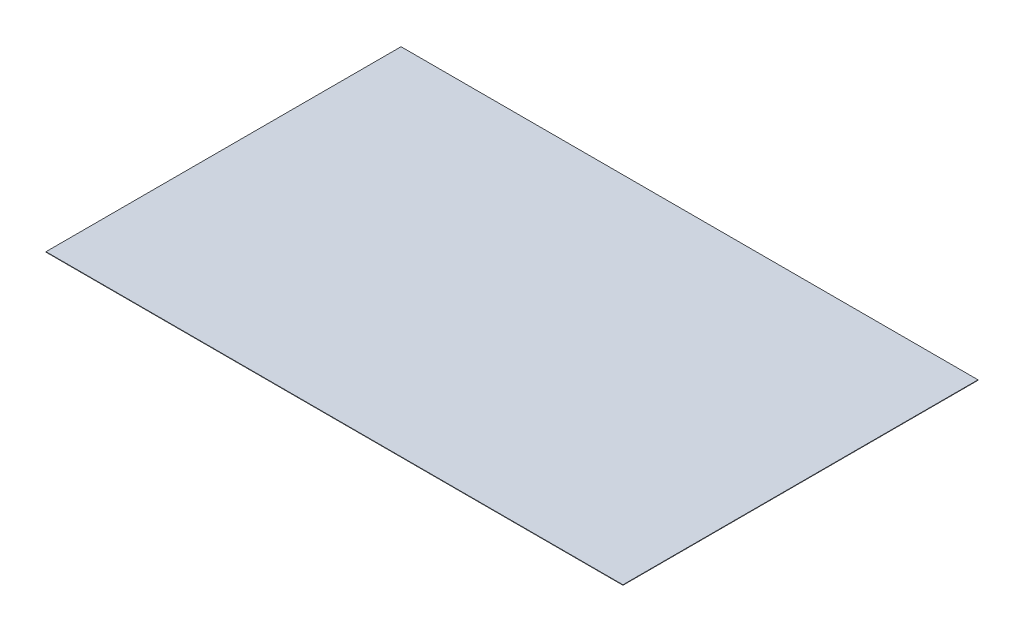
SolidWorks part; units mm, degrees
ref_plane "Front Plane" through (0, 0, 0) normal (0, 0, 1) x (1, 0, 0)
ref_plane "Top Plane" through (0, 0, 0) normal (0, 1, 0) x (1, 0, 0)
ref_plane "Right Plane" through (0, 0, 0) normal (1, 0, 0) x (0, 0, -1)
sketch "Sketch1" plane through (0, 0, 0) normal (0, 1, 0) x (1, 0, 0)
  line L1 (-6500, 4000) -> (6500, 4000)
  line L2 (-6500, 4000) -> (-6500, -4000)
  line L3 (-6500, -4000) -> (6500, -4000)
  line L4 (6500, 4000) -> (6500, -4000)
  line L5 (-6500, 4000) -> (6500, -4000) construction
  line L6 (-6500, -4000) -> (6500, 4000) construction
  point P0 (0, 0)
  dimension "D1" = 13000
  dimension "D2" = 8000
extrude "Boss-Extrude1" add sketch "Sketch1" along normal blind 10
